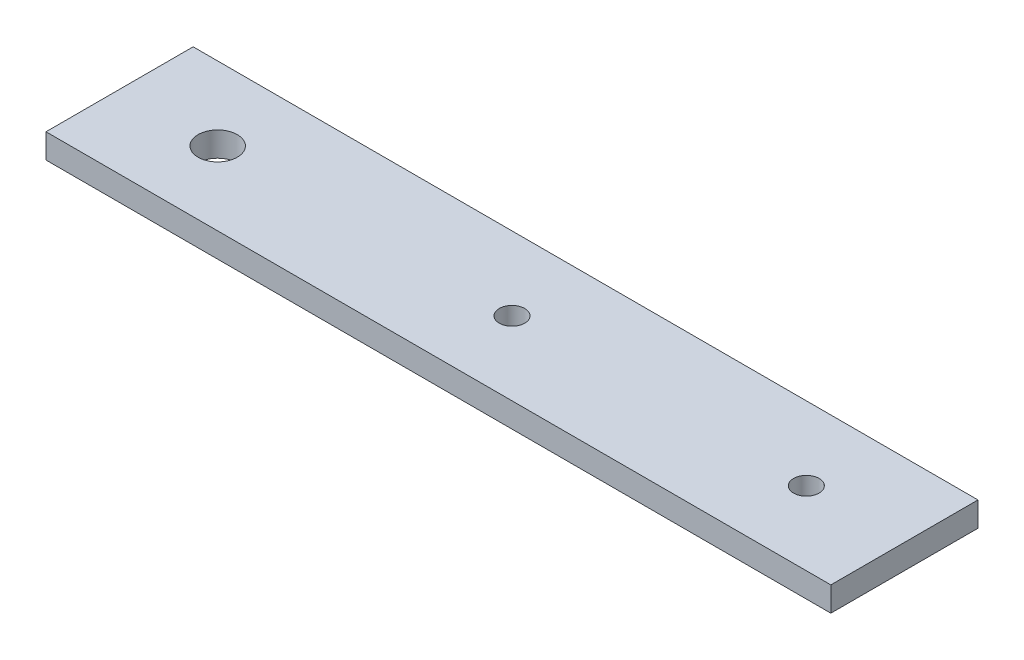
SolidWorks part; units mm, degrees
material "PW40:6:Ar:0:-1:Re:14:Ts:15:16:17:18:19:20:Tl:21:22:23:24:25:26:27:28:29:"
ref_plane "Front" through (0, 0, 0) normal (0, 0, 1) x (1, 0, 0)
ref_plane "Top" through (0, 0, 0) normal (0, 1, 0) x (1, 0, 0)
ref_plane "Right" through (0, 0, 0) normal (1, 0, 0) x (0, 0, -1)
sketch "Sketch1" plane through (0, 0, 0) normal (0, 1, 0) x (1, 0, 0)
  line L0 (0, 0) -> (101.6, 0)
  line L1 (0, 0) -> (0, 19.05)
  line L2 (101.6, 19.05) -> (0, 19.05)
  line L3 (101.6, 19.05) -> (101.6, 0)
  circle A0 centre (12.7, 9.525) radius 2.54
  circle A1 centre (50.8, 9.525) radius 1.651
  circle A2 centre (88.9, 9.525) radius 1.651
  point P11 (101.6, 9.525)
  dimension "D3" = 3.302
  dimension "D7" = 5.08
  dimension "D1" = 101.6
  dimension "D2" = 19.05
  dimension "D4" = 38.1
  dimension "D5" = 12.7
  dimension "D6" = 12.7
extrude "Base-Extrude" add sketch "Sketch1" along normal blind 3.175
